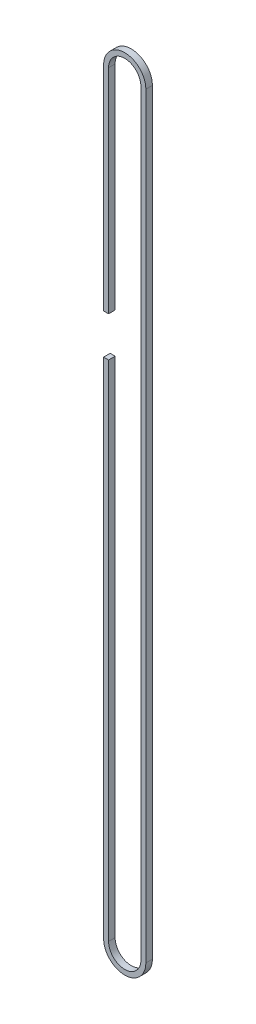
SolidWorks part; units mm, degrees
material "Cast Alloy Steel"
ref_plane "Front Plane" through (0, 0, 0) normal (0, 0, 1) x (1, 0, 0)
ref_plane "Top Plane" through (0, 0, 0) normal (0, 1, 0) x (1, 0, 0)
ref_plane "Right Plane" through (0, 0, 0) normal (1, 0, 0) x (0, 0, -1)
sketch "Sketch1" plane through (0, 0, 0) normal (0, 0, 1) x (1, 0, 0)
  line L0 (-25.1587, 901.7) -> (-25.1587, 647.7)
  line L1 (25.1587, 0) -> (25.1587, 901.7)
  line L2 (19.2659, 0) -> (19.2659, 901.7)
  line L3 (-19.2659, 901.7) -> (-19.2659, 647.7)
  line L4 (-25.1587, 647.7) -> (-19.2659, 647.7)
  line L5 (-19.2659, 600.075) -> (-25.1587, 600.075)
  line L6 (-25.1587, 600.075) -> (-25.1587, 0)
  line L7 (-25.1587, 901.7) -> (-25.1587, 0) construction
  line L8 (-19.2659, 600.075) -> (-19.2659, 0)
  line L9 (-19.2659, 901.7) -> (-19.2659, 0) construction
  circle A0 centre (0, 0) radius 25.1587 construction
  circle A1 centre (0, 901.7) radius 25.1587 construction
  arc A2 (-25.1587, 901.7) -> (25.1587, 901.7) centre (0, 901.7) cw
  arc A3 (-25.1587, 0) -> (25.1587, 0) centre (0, 0) ccw
  arc A4 (-19.2659, 901.7) -> (19.2659, 901.7) centre (0, 901.7) cw
  arc A5 (-19.2659, 0) -> (19.2659, 0) centre (0, 0) ccw
  dimension "D2" = 50.3174
  dimension "D1" = 901.7
  dimension "D4" = 47.625
  dimension "D5" = 254
  dimension "D3" = 5.8928
extrude "Boss-Extrude1" add sketch "Sketch1" along normal mid plane 7.7978
